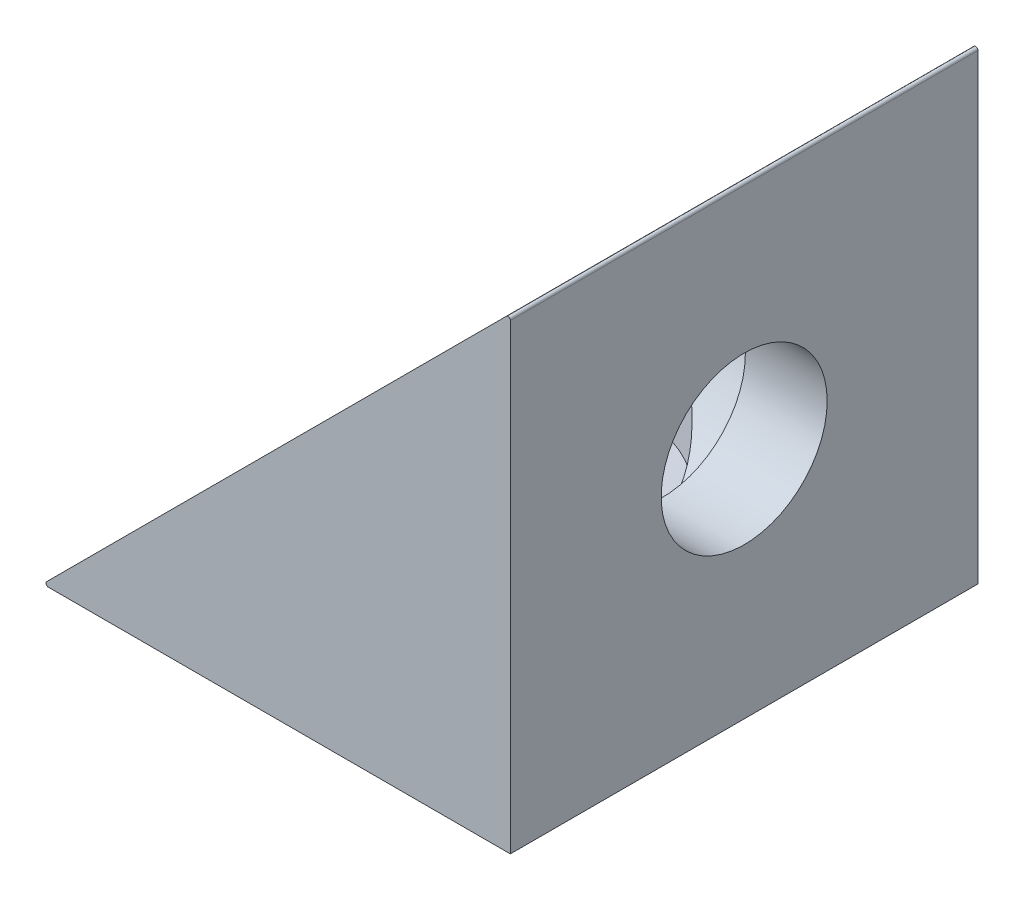
SolidWorks part; units mm, degrees
material "6063-T6"
ref_plane "Plan de face" through (0, 0, 0) normal (0, 0, 1) x (1, 0, 0)
ref_plane "Plan de dessus" through (0, 0, 0) normal (0, 1, 0) x (1, 0, 0)
ref_plane "Plan de droite" through (0, 0, 0) normal (1, 0, 0) x (0, 0, -1)
sketch "Esquisse1" plane through (0, 0, 0) normal (0, 0, 1) x (1, 0, 0)
  line L0 (-20, -20) -> (0, 0)
  line L1 (-20, -20) -> (0, -20)
  line L4 (0, -20) -> (0, 0)
  line L5 (-20, -20) -> (0, 0) construction
  point P0 (0, 0)
  dimension "D1" = 20
  dimension "D2" = 20
extrude "Boss.-Extru.1" add sketch "Esquisse1" along normal blind 20
sketch "Esquisse2" plane through (0, -20, 0) normal (0, -1, 0) x (1, 0, 0)
  line L0 (-20, 10) -> (0, 10) construction
  line L1 (-20, 20) -> (-20, 0) construction
  line L2 (0, 20) -> (0, 0) construction
  line L3 (-10, 20) -> (-10, 0) construction
  line L4 (-20, 20) -> (0, 20) construction
  line L5 (-20, 0) -> (0, 0) construction
  circle A0 centre (-10, 10) radius 3.55
  dimension "D1" = 7.1
extrude "Enlèv. mat.-Extru.1" cut sketch "Esquisse2" against normal through all
sketch "Esquisse3" plane through (0, 0, 0) normal (1, 0, 0) x (0, 0, 1)
  line L0 (0, 10) -> (20, 10) construction
  line L3 (10, 20) -> (10, 0) construction
  line L6 (20, 20) -> (20, 0) construction
  line L7 (0, 20) -> (0, 0) construction
  line L8 (20, 20) -> (0, 20) construction
  circle A0 centre (10, 10) radius 3.55
  dimension "D1" = 7.1
extrude "Enlèv. mat.-Extru.2" cut sketch "Esquisse3" against normal through all
sketch "Esquisse4" plane through (0, 0, 0) normal (1, 0, 0) x (0, 0, -1)
  circle A0 centre (-10, -10) radius 5.5
  dimension "D1" = 11
extrude "Enlèv. mat.-Extru.3" cut sketch "Esquisse4" against normal through all from offset 3.5 offset against normal yes
sketch "Esquisse5" plane through (0, -20, 0) normal (0, -1, 0) x (1, 0, 0)
  circle A0 centre (-10, 10) radius 5.5
  dimension "D1" = 11
extrude "Enlèv. mat.-Extru.4" cut sketch "Esquisse5" against normal through all from offset 3.5 offset against normal yes
fillet "Congé1" radius 0.1 2 edges at (0, 0, 10) (-20, -20, 10)
